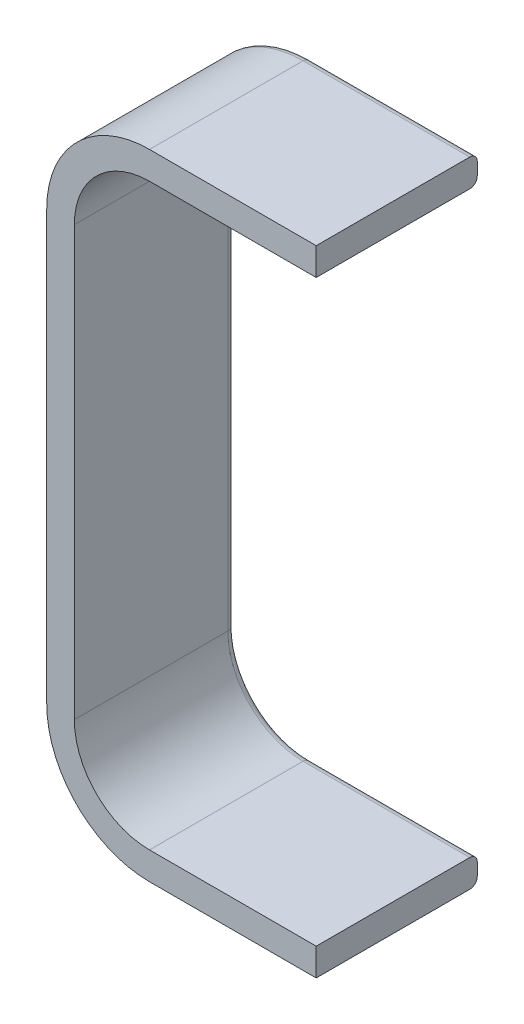
SolidWorks part; units mm, degrees
material "Chêne"
ref_plane "Plan de face" through (0, 0, 0) normal (0, 0, 1) x (1, 0, 0)
ref_plane "Plan de dessus" through (0, 0, 0) normal (0, 1, 0) x (1, 0, 0)
ref_plane "Plan de droite" through (0, 0, 0) normal (1, 0, 0) x (0, 0, -1)
sketch "Esquisse1" plane through (0, 0, 0) normal (0, 0, 1) x (1, 0, 0)
  line L0 (-193, -82) -> (-133, -82) construction
  line L1 (-133, -82) -> (-133, -22) construction
  line L2 (-133, -22) -> (0, -22)
  line L3 (0, -22) -> (0, 0)
  line L4 (0, 0) -> (-133, 0)
  line L5 (-215, -82) -> (-215, -424)
  line L6 (-193, -82) -> (-193, -424)
  line L7 (-133, -506) -> (0, -506)
  line L8 (0, -506) -> (0, -484)
  line L10 (0, -484) -> (-133, -484)
  arc A2 (-133, -22) -> (-193, -82) centre (-133, -82) ccw
  arc A3 (-215, -82) -> (-133, 0) centre (-133, -82) cw
  arc A4 (-193, -424) -> (-133, -484) centre (-133, -424) ccw
  arc A5 (-215, -424) -> (-133, -506) centre (-133, -424) ccw
  dimension "D6" = 60
  dimension "D7" = 133
  dimension "D8" = 60
  dimension "D1" = 22
  dimension "D2" = 193
  dimension "D4" = 462
  dimension "D5" = 22
extrude "Boss.-Extru.1" add sketch "Esquisse1" against normal blind 128.5
fillet "Congé1" radius 6 10 edges at (-66.5, -22, -128.5) (-175.4264, -39.5736, -128.5) (-193, -253, -128.5) (-66.5, -484, -128.5) (-66.5, 0, -128.5) (-190.9828, -24.0172, -128.5) (-215, -253, -128.5) (-190.9828, -481.9828, -128.5) (-175.4264, -466.4264, -128.5) (-66.5, -506, -128.5)
